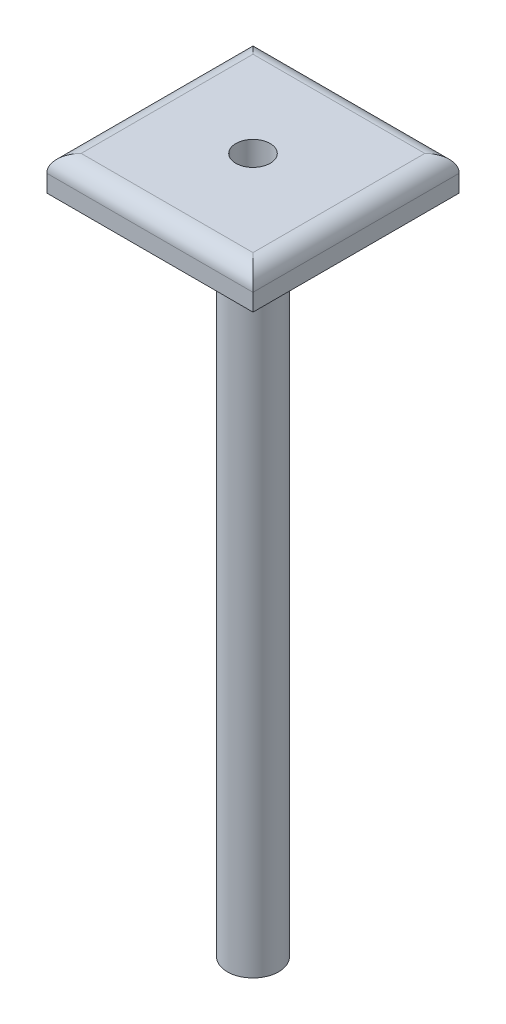
SolidWorks part; units mm, degrees
ref_plane "Front Plane" through (0, 0, 0) normal (0, 0, 1) x (1, 0, 0)
ref_plane "Top Plane" through (0, 0, 0) normal (0, 1, 0) x (1, 0, 0)
ref_plane "Right Plane" through (0, 0, 0) normal (1, 0, 0) x (0, 0, -1)
sketch "Sketch1" plane through (0, 0, 0) normal (0, 1, 0) x (1, 0, 0)
  line L1 (-15.24, 15.24) -> (15.24, 15.24)
  line L2 (-15.24, 15.24) -> (-15.24, -15.24)
  line L3 (-15.24, -15.24) -> (15.24, -15.24)
  line L4 (15.24, 15.24) -> (15.24, -15.24)
  line L5 (-15.24, 15.24) -> (15.24, -15.24) construction
  line L6 (-15.24, -15.24) -> (15.24, 15.24) construction
  point P0 (0, 0)
  dimension "D1" = 30.48
extrude "Boss-Extrude1" add sketch "Sketch1" along normal blind 5.08
fillet "Fillet1" radius 2.54 4 edges at (0, 5.08, 15.24) (-15.24, 5.08, 0) (0, 5.08, -15.24) (15.24, 5.08, 0)
sketch "Sketch2" plane through (0, 0, 0) normal (0, -1, 0) x (1, 0, 0)
  circle A0 centre (0, 0) radius 3.81
  dimension "D1" = 7.62
extrude "Boss-Extrude2" add sketch "Sketch2" along normal blind 97.79
sketch "Sketch3" plane through (0, 5.08, 0) normal (0, 1, 0) x (1, 0, 0)
  circle A0 centre (0, 0) radius 2.54
  dimension "D1" = 5.08
extrude "Cut-Extrude1" cut sketch "Sketch3" against normal blind 101.6
